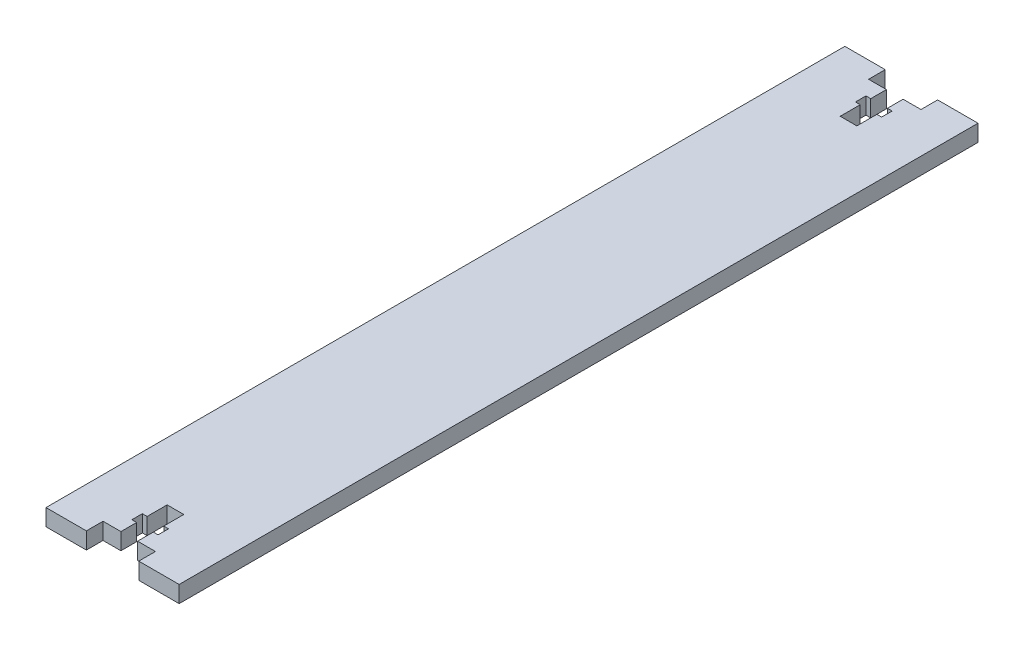
SolidWorks part; units mm, degrees
ref_plane "Front Plane" through (0, 0, 0) normal (0, 0, 1) x (1, 0, 0)
ref_plane "Top Plane" through (0, 0, 0) normal (0, 1, 0) x (1, 0, 0)
ref_plane "Right Plane" through (0, 0, 0) normal (1, 0, 0) x (0, 0, -1)
sketch "Sketch1" plane through (0, 0, 0) normal (0, 1, 0) x (1, 0, 0)
  line L1 (12.7, 76.2) -> (-12.7, 76.2)
  line L2 (12.7, 76.2) -> (12.7, -76.2)
  line L3 (12.7, -76.2) -> (-12.7, -76.2)
  line L4 (-12.7, 76.2) -> (-12.7, -76.2)
  line L5 (12.7, 76.2) -> (-12.7, -76.2) construction
  line L6 (12.7, -76.2) -> (-12.7, 76.2) construction
  point P0 (0, 0)
  dimension "D1" = 25.4
  dimension "D2" = 152.4
extrude "Boss-Extrude1" add sketch "Sketch1" along normal blind 3.18
sketch "Sketch2" plane through (0, 3.18, 0) normal (0, 1, 0) x (1, 0, 0)
  line L0 (12.7, 76.2) -> (-12.7, 76.2) construction
  line L1 (-1.59, 76.2) -> (1.59, 76.2)
  line L2 (-1.59, 73.02) -> (-1.59, 70.02)
  line L3 (0, 64.2) -> (1.59, 64.2)
  line L4 (1.59, 73.02) -> (1.59, 70.02)
  line L5 (0, 64.2) -> (0, -64.2) construction
  line L6 (1.59, 73.02) -> (5, 73.02)
  line L7 (-5, 76.2) -> (5, 76.2)
  line L8 (-5, 76.2) -> (-5, 73.02)
  line L9 (-5, 73.02) -> (-1.59, 73.02)
  line L10 (5, 76.2) -> (5, 73.02)
  line L11 (-2.5, 70.02) -> (-1.59, 70.02)
  line L12 (-2.5, 70.02) -> (-2.5, 68.02)
  line L13 (-2.5, 68.02) -> (-1.59, 68.02)
  line L14 (2.5, 70.02) -> (2.5, 68.02)
  line L15 (1.59, 70.02) -> (2.5, 70.02)
  line L16 (1.59, 68.02) -> (2.5, 68.02)
  line L17 (-1.59, 68.02) -> (-1.59, 64.2)
  line L18 (1.59, 68.02) -> (1.59, 64.2)
  line L19 (12.7, 0) -> (-12.7, 0) construction
  line L20 (12.7, -76.2) -> (12.7, 76.2) construction
  line L21 (-12.7, 76.2) -> (-12.7, -76.2) construction
  line L22 (0, 64.2) -> (-1.59, 64.2)
  line L23 (0, -64.2) -> (-1.59, -64.2)
  line L24 (1.59, -68.02) -> (1.59, -64.2)
  line L25 (-1.59, -68.02) -> (-1.59, -64.2)
  line L26 (1.59, -68.02) -> (2.5, -68.02)
  line L27 (1.59, -70.02) -> (2.5, -70.02)
  line L28 (2.5, -70.02) -> (2.5, -68.02)
  line L29 (-2.5, -68.02) -> (-1.59, -68.02)
  line L30 (-2.5, -70.02) -> (-2.5, -68.02)
  line L31 (-2.5, -70.02) -> (-1.59, -70.02)
  line L32 (5, -76.2) -> (5, -73.02)
  line L33 (-5, -73.02) -> (-1.59, -73.02)
  line L34 (-5, -76.2) -> (-5, -73.02)
  line L35 (-5, -76.2) -> (5, -76.2)
  line L36 (1.59, -73.02) -> (5, -73.02)
  line L37 (1.59, -73.02) -> (1.59, -70.02)
  line L38 (0, -64.2) -> (1.59, -64.2)
  line L39 (-1.59, -73.02) -> (-1.59, -70.02)
  line L40 (-1.59, -76.2) -> (1.59, -76.2)
  point P30 (0, 0)
  line M22 (12.7, 76.2) -> (-12.7, 76.2)
  dimension "D1" = 3.18
  dimension "D2" = 12
  dimension "D3" = 10
  dimension "D4" = 3.18
  dimension "D5" = 3
  dimension "D6" = 5
  dimension "D7" = 2
extrude "Cut-Extrude1" cut sketch "Sketch2" against normal blind 3.18 contours L5 L7 L8 L9 L2 L11 L12 L13 L17 L3 M22 | L23 L25 L29 L30 L31 L39 L33 L34 L35 L32 L36 L37 L27 L28 L26 L24 L38
